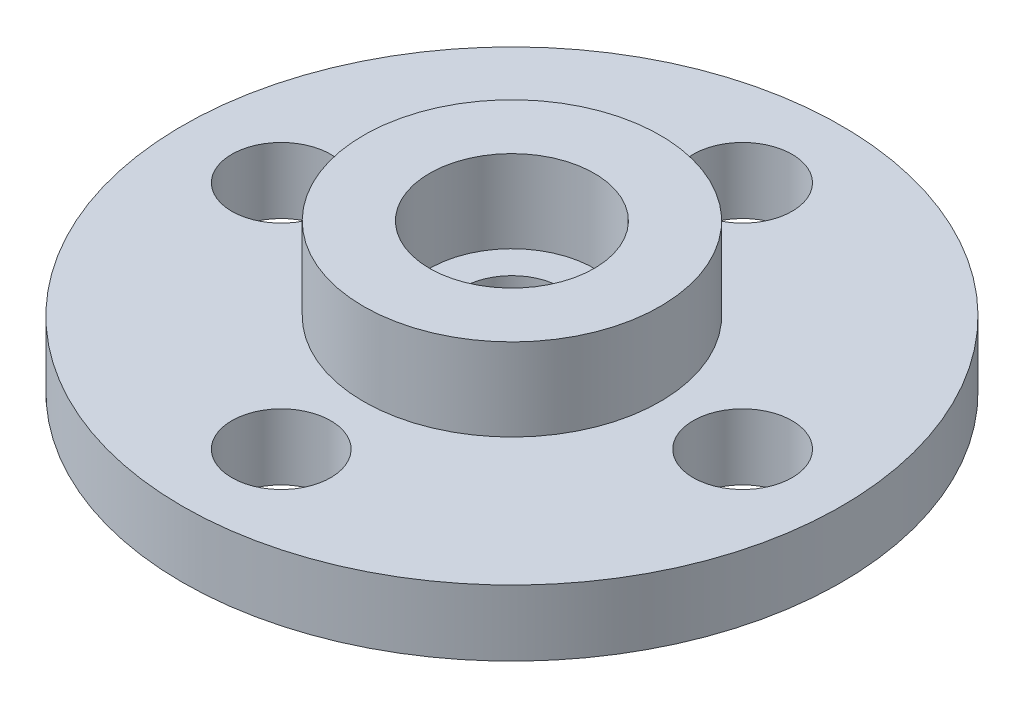
SolidWorks part; units mm, degrees
ref_plane "前视基准面" through (0, 0, 0) normal (0, 0, 1) x (1, 0, 0)
ref_plane "上视基准面" through (0, 0, 0) normal (0, 1, 0) x (1, 0, 0)
ref_plane "右视基准面" through (0, 0, 0) normal (1, 0, 0) x (0, 0, -1)
sketch "草图1" plane through (0, 0, 0) normal (0, 1, 0) x (1, 0, 0)
  circle A0 centre (0, 0) radius 10
extrude "凸台-拉伸1" add sketch "草图1" along normal blind 2
sketch "草图2" plane through (0, 2, 0) normal (0, 1, 0) x (1, 0, 0)
  circle A0 centre (0, 0) radius 1.5
  circle A1 centre (0, 7) radius 1.5
  circle A2 centre (7, 0) radius 1.5
  circle A3 centre (0, -7) radius 1.5
  circle A4 centre (-7, 0) radius 1.5
  point P14 (0, 0)
  dimension "D1" = 4
  dimension "D2" = 7
extrude "切除-拉伸1" cut sketch "草图2" against normal blind 2
sketch "草图3" plane through (0, 2, 0) normal (0, 1, 0) x (1, 0, 0)
  circle A0 centre (0, 0) radius 2.5
  circle A1 centre (0, 0) radius 4.5
extrude "凸台-拉伸2" add sketch "草图3" along normal blind 2.5
